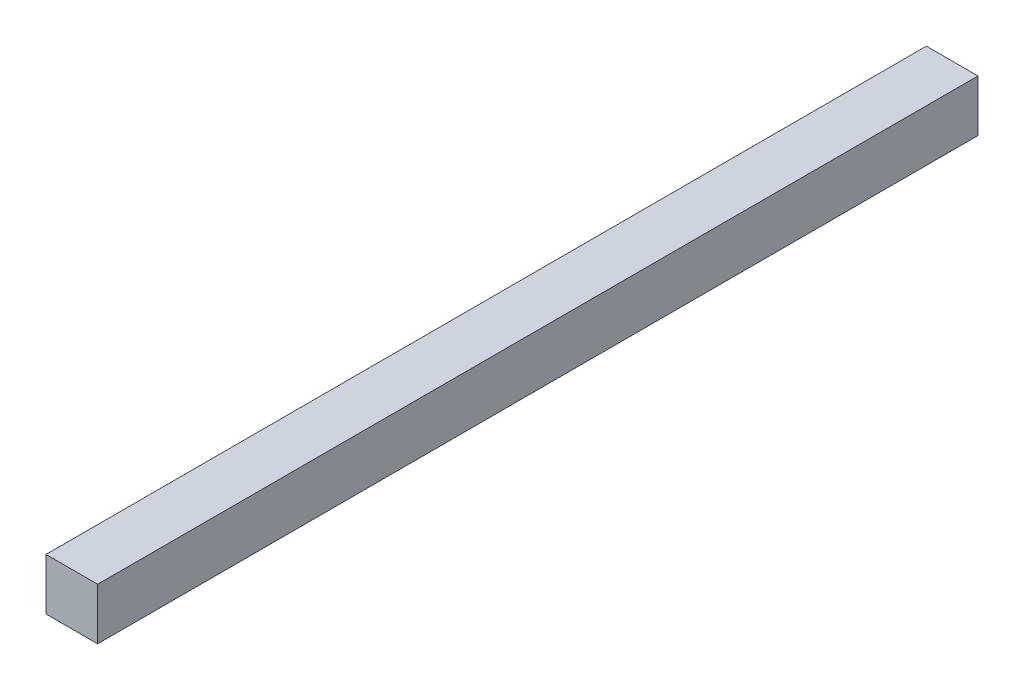
SolidWorks part; units mm, degrees
material "ASTM A36 Steel"
ref_plane "Front Plane" through (0, 0, 0) normal (0, 0, 1) x (1, 0, 0)
ref_plane "Top Plane" through (0, 0, 0) normal (0, 1, 0) x (1, 0, 0)
ref_plane "Right Plane" through (0, 0, 0) normal (1, 0, 0) x (0, 0, -1)
sketch "Sketch1" plane through (0, 0, 0) normal (0, 0, 1) x (1, 0, 0)
  line L1 (0, 0) -> (3.556, 0)
  line L2 (0, 0) -> (0, -3.556)
  line L3 (0, -3.556) -> (3.556, -3.556)
  line L4 (3.556, 0) -> (3.556, -3.556)
  dimension "D1" = 3.556
  dimension "D2" = 3.556
extrude "Boss-Extrude1" add sketch "Sketch1" along normal blind 60.6425
